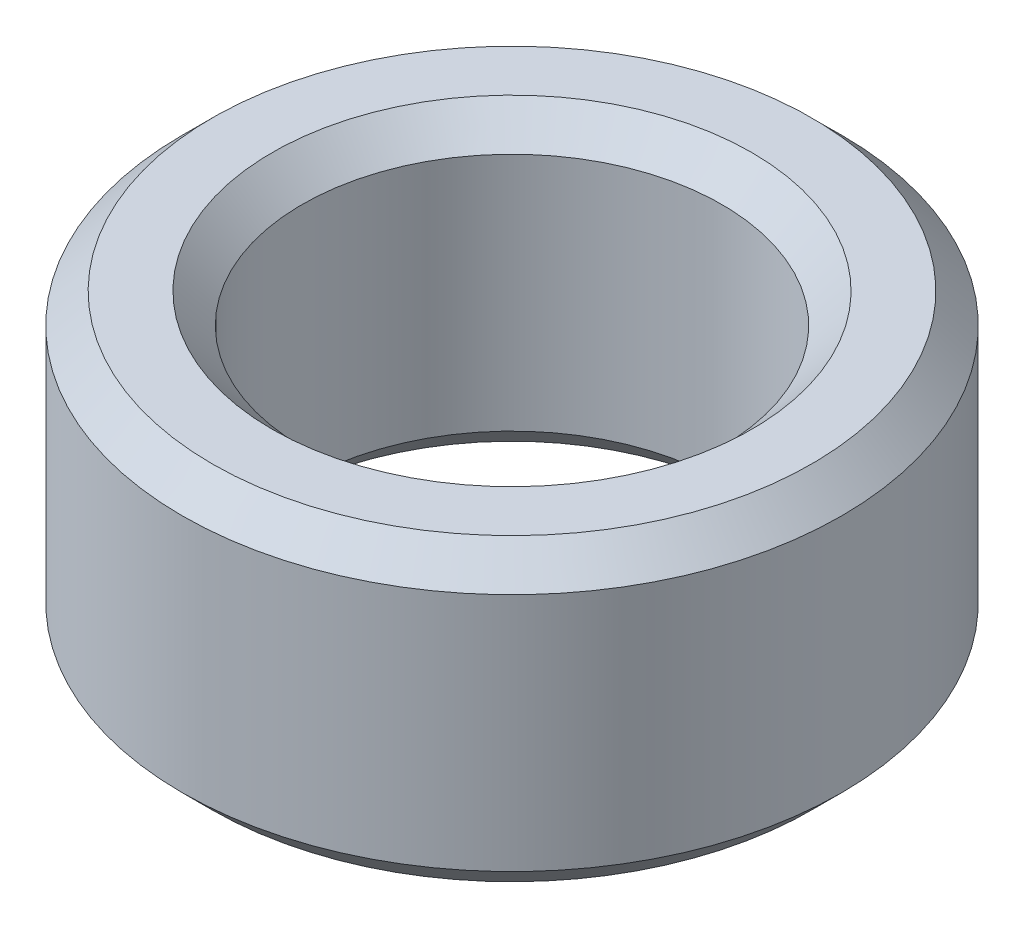
SolidWorks part; units mm, degrees
ref_plane "Front Plane" through (0, 0, 0) normal (0, 0, 1) x (1, 0, 0)
ref_plane "Top Plane" through (0, 0, 0) normal (0, 1, 0) x (1, 0, 0)
ref_plane "Right Plane" through (0, 0, 0) normal (1, 0, 0) x (0, 0, -1)
sketch "Sketch2" plane through (0, 0, 0) normal (0, 1, 0) x (1, 0, 0)
  circle A0 centre (0, 0) radius 1.75
  circle A1 centre (0, 0) radius 2.75
  dimension "D1" = 3.5
  dimension "D2" = 1
extrude "Boss-Extrude1" add sketch "Sketch2" along normal blind 2.5
chamfer "Chamfer1" distance 0.25 1 edges at (0, 2.5, 2.75)
chamfer "Chamfer2" distance 0.25 angle 45 1 edges at (0, 0, 2.75)
chamfer "Chamfer3" distance 0.25 angle 45 1 edges at (0, 2.5, 1.75)
chamfer "Chamfer4" distance 0.25 angle 45 1 edges at (0, 0, 1.75)
